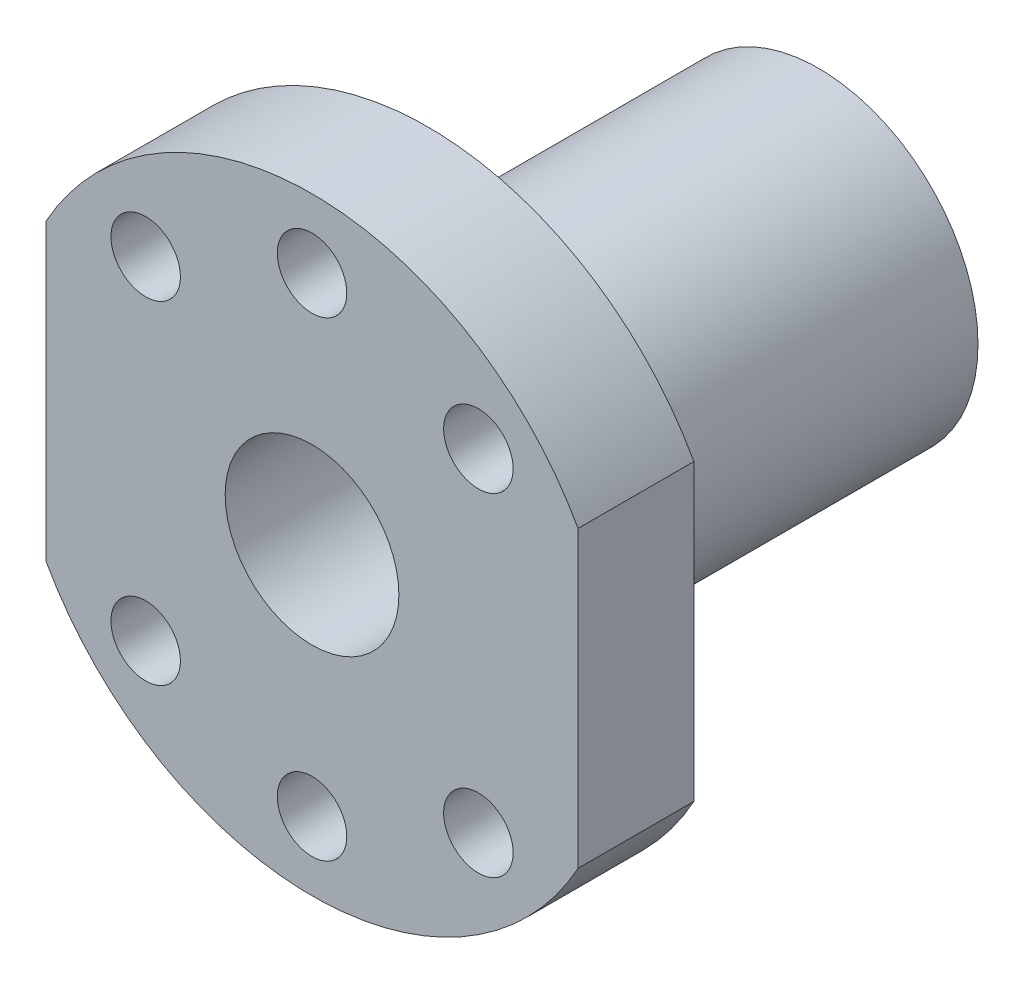
SolidWorks part; units mm, degrees
ref_plane "Front Plane" through (0, 0, 0) normal (0, 0, 1) x (1, 0, 0)
ref_plane "Top Plane" through (0, 0, 0) normal (0, 1, 0) x (1, 0, 0)
ref_plane "Right Plane" through (0, 0, 0) normal (1, 0, 0) x (0, 0, -1)
sketch "Sketch1" plane through (0, 0, 0) normal (0, 0, 1) x (1, 0, 0)
  line L0 (-18.375, 10.1666) -> (-18.375, -10.1666)
  line L1 (18.375, 10.1666) -> (18.375, -10.1666)
  arc A0 (-18.375, -10.1666) -> (18.375, -10.1666) centre (0, 0) ccw
  circle A1 centre (0, 0) radius 6
  arc A2 (18.375, 10.1666) -> (-18.375, 10.1666) centre (0, 0) ccw
  dimension "D1" = 21
  dimension "D2" = 12
  dimension "D3" = 18.375
  dimension "D4" = 18.375
extrude "Boss-Extrude1" add sketch "Sketch1" along normal mid plane 8
sketch "Sketch2" plane through (0, 0, 4) normal (0, 0, 1) x (1, 0, 0)
  line L0 (0, 0) -> (0, -28.8365) construction
  line L1 (0, 0) -> (27.189, 27.189) construction
  line L2 (0, 0) -> (-27.231, 27.231) construction
  circle A0 centre (0, 0) radius 16.25 construction
  circle A1 centre (-11.4905, 11.4905) radius 2.4
  circle A2 centre (0, 16.25) radius 2.4
  circle A3 centre (11.4905, 11.4905) radius 2.4
  circle A4 centre (11.4905, -11.4905) radius 2.4
  circle A5 centre (0, -16.25) radius 2.4
  circle A6 centre (-11.4905, -11.4905) radius 2.4
  dimension "D1" = 32.5
  dimension "D4" = 4.8
  dimension "D5" = 4.8
  dimension "D6" = 4.8
  dimension "D7" = 4.8
  dimension "D8" = 4.8
  dimension "D9" = 4.8
  dimension "D2" = 45
  dimension "D3" = 45
extrude "Cut-Extrude1" cut sketch "Sketch2" against normal through all
sketch "Sketch3" plane through (0, 0, -4) normal (0, 0, -1) x (-1, 0, 0)
  circle A0 centre (0, 0) radius 11
  circle A1 centre (0, 0) radius 6
  dimension "D1" = 12
  dimension "D2" = 22
extrude "Boss-Extrude2" add sketch "Sketch3" along normal blind 27
equation "\"D3@Sketch1\"=36.75/2"
equation "\"D4@Sketch1\"=\"D3@Sketch1\""
